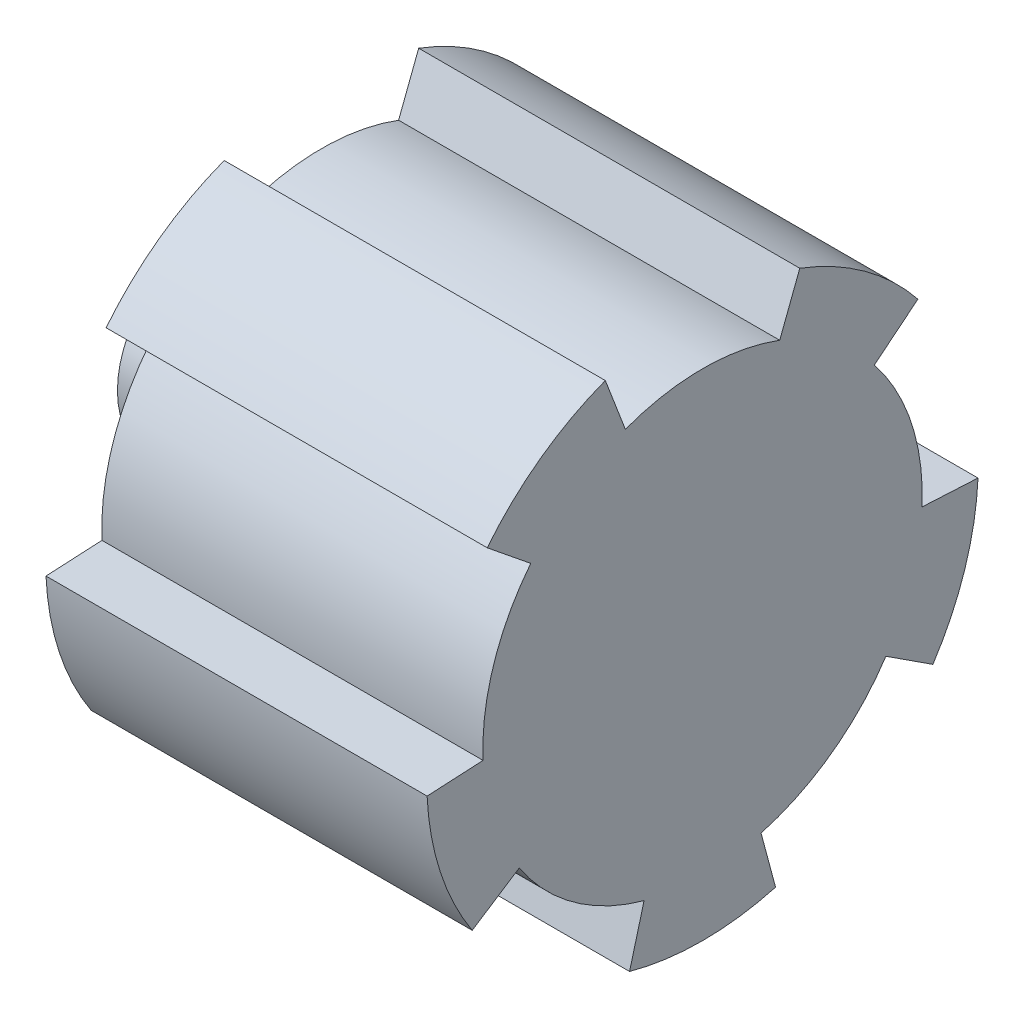
SolidWorks part; units mm, degrees
ref_plane "Front Plane" through (0, 0, 0) normal (0, 0, 1) x (1, 0, 0)
ref_plane "Top Plane" through (0, 0, 0) normal (0, 1, 0) x (1, 0, 0)
ref_plane "Right Plane" through (0, 0, 0) normal (1, 0, 0) x (0, 0, -1)
sketch "Sketch1" plane through (-18, 0, 0) normal (-1, 0, 0) x (0, 0, 1)
  line L10 (-9.9969, -0.2484) -> (-12.4935, -0.3793)
  line L11 (-10.3304, -7.0367) -> (-8.2337, -5.6751)
  line L12 (-2.853, -9.5844) -> (-3.5, -11.9992)
  line L13 (3.5, -11.9992) -> (2.853, -9.5844)
  line L14 (8.2337, -5.6751) -> (10.3304, -7.0367)
  line L15 (12.4935, -0.3793) -> (9.9969, -0.2484)
  line L16 (7.9417, 6.077) -> (9.8845, 7.6503)
  line L17 (4.2214, 11.7648) -> (3.3255, 9.4309)
  line L18 (-3.3255, 9.4309) -> (-4.2214, 11.7648)
  line L19 (-9.8845, 7.6503) -> (-7.9417, 6.077)
  line L20 (-9.9969, -0.2484) -> (-12.4935, -0.3793) construction
  line L21 (-10.3304, -7.0367) -> (-8.2337, -5.6751) construction
  line L22 (-2.853, -9.5844) -> (-3.5, -11.9992) construction
  line L23 (3.5, -11.9992) -> (2.853, -9.5844) construction
  line L24 (8.2337, -5.6751) -> (10.3304, -7.0367) construction
  line L25 (12.4935, -0.3793) -> (9.9969, -0.2484) construction
  line L26 (7.9417, 6.077) -> (9.8845, 7.6503) construction
  line L27 (4.2214, 11.7648) -> (3.3255, 9.4309) construction
  line L28 (-3.3255, 9.4309) -> (-4.2214, 11.7648) construction
  line L29 (-9.8845, 7.6503) -> (-7.9417, 6.077) construction
  line L30 (-3.4418, 9.1757) -> (-4.3374, 11.509)
  line L31 (-9.6054, 7.6816) -> (-7.6631, 6.1088)
  line L32 (-9.7902, -0.4379) -> (-12.2861, -0.5687)
  line L33 (-10.2739, -6.7615) -> (-8.1778, -5.4003)
  line L34 (-2.6089, -9.4464) -> (-3.2558, -11.8605)
  line L35 (3.2558, -11.8605) -> (2.6089, -9.4464)
  line L36 (8.1778, -5.4003) -> (10.2739, -6.7615)
  line L37 (12.2861, -0.5687) -> (9.7902, -0.4379)
  line L38 (7.6631, 6.1088) -> (9.6054, 7.6816)
  line L39 (4.3374, 11.509) -> (3.4418, 9.1757)
  arc A10 (-7.9417, 6.077) -> (-9.9969, -0.2484) centre (0, 0) ccw
  arc A11 (-12.4935, -0.3793) -> (-10.3304, -7.0367) centre (0, 0) ccw
  arc A12 (-8.2337, -5.6751) -> (-2.853, -9.5844) centre (0, 0) ccw
  arc A13 (-3.5, -11.9992) -> (3.5, -11.9992) centre (0, 0) ccw
  arc A14 (2.853, -9.5844) -> (8.2337, -5.6751) centre (0, 0) ccw
  arc A15 (10.3304, -7.0367) -> (12.4935, -0.3793) centre (0, 0) ccw
  arc A16 (9.9969, -0.2484) -> (7.9417, 6.077) centre (0, 0) ccw
  arc A17 (9.8845, 7.6503) -> (4.2214, 11.7648) centre (0, 0) ccw
  arc A18 (3.3255, 9.4309) -> (-3.3255, 9.4309) centre (0, 0) ccw
  arc A19 (-4.2214, 11.7648) -> (-9.8845, 7.6503) centre (0, 0) ccw
  arc A20 (-7.9417, 6.077) -> (-9.9969, -0.2484) centre (0, 0) ccw construction
  arc A21 (-12.4935, -0.3793) -> (-10.3304, -7.0367) centre (0, 0) ccw construction
  arc A22 (-8.2337, -5.6751) -> (-2.853, -9.5844) centre (0, 0) ccw construction
  arc A23 (-3.5, -11.9992) -> (3.5, -11.9992) centre (0, 0) ccw construction
  arc A24 (2.853, -9.5844) -> (8.2337, -5.6751) centre (0, 0) ccw construction
  arc A25 (10.3304, -7.0367) -> (12.4935, -0.3793) centre (0, 0) ccw construction
  arc A26 (9.9969, -0.2484) -> (7.9417, 6.077) centre (0, 0) ccw construction
  arc A27 (9.8845, 7.6503) -> (4.2214, 11.7648) centre (0, 0) ccw construction
  arc A28 (3.3255, 9.4309) -> (-3.3255, 9.4309) centre (0, 0) ccw construction
  arc A29 (-4.2214, 11.7648) -> (-9.8845, 7.6503) centre (0, 0) ccw construction
  arc A30 (-4.3374, 11.509) -> (-9.6054, 7.6816) centre (0, 0) ccw
  arc A31 (-7.6631, 6.1088) -> (-9.7902, -0.4379) centre (0, 0) ccw
  arc A32 (-12.2861, -0.5687) -> (-10.2739, -6.7615) centre (0, 0) ccw
  arc A33 (-8.1778, -5.4003) -> (-2.6089, -9.4464) centre (0, 0) ccw
  arc A34 (-3.2558, -11.8605) -> (3.2558, -11.8605) centre (0, 0) ccw
  arc A35 (2.6089, -9.4464) -> (8.1778, -5.4003) centre (0, 0) ccw
  arc A36 (10.2739, -6.7615) -> (12.2861, -0.5687) centre (0, 0) ccw
  arc A37 (9.7902, -0.4379) -> (7.6631, 6.1088) centre (0, 0) ccw
  arc A38 (9.6054, 7.6816) -> (4.3374, 11.509) centre (0, 0) ccw
  arc A39 (3.4418, 9.1757) -> (-3.4418, 9.1757) centre (0, 0) ccw
  dimension "D1" = 0
  dimension "D3" = 0.2
extrude "KeyedBody" add sketch "Sketch1" along normal blind 17
sketch "Sketch2" plane through (-35, 0, 0) normal (-1, 0, 0) x (0, 0, 1)
  circle A0 centre (0, 0) radius 4.1
  dimension "D1" = 8.2
extrude "SmallShaft" add sketch "Sketch2" along normal blind 5
